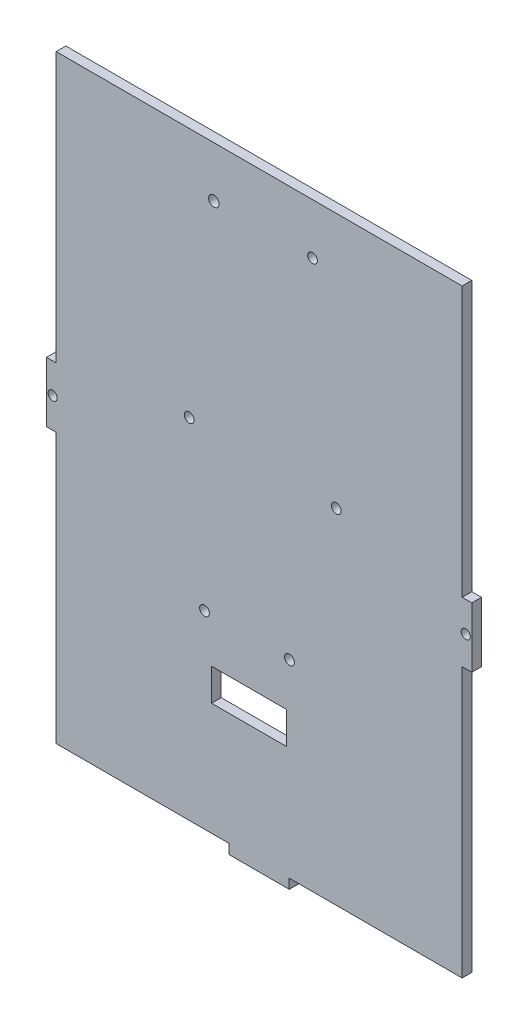
SolidWorks part; units mm, degrees
ref_plane "Front Plane" through (0, 0, 0) normal (0, 0, 1) x (1, 0, 0)
ref_plane "Top Plane" through (0, 0, 0) normal (0, 1, 0) x (1, 0, 0)
ref_plane "Right Plane" through (0, 0, 0) normal (1, 0, 0) x (0, 0, -1)
sketch "Sketch1" plane through (0, 0, 0) normal (0, 0, 1) x (1, 0, 0)
  line L1 (-69.85, 101.6) -> (69.85, 101.6)
  line L2 (-69.85, 101.6) -> (-69.85, -101.6)
  line L3 (-69.85, -101.6) -> (69.85, -101.6)
  line L4 (69.85, 101.6) -> (69.85, -101.6)
  line L5 (-69.85, 101.6) -> (69.85, -101.6) construction
  line L6 (-69.85, -101.6) -> (69.85, 101.6) construction
  point P0 (0, 0)
  dimension "D1" = 203.2
  dimension "D2" = 139.7
extrude "Boss-Extrude1" add sketch "Sketch1" along normal blind 3.18
sketch "Sketch2" plane through (0, 0, 3.18) normal (0, 0, 1) x (1, 0, 0)
  line L0 (0, 0) -> (69.85, 0) construction
  line L1 (-10, 101.6) -> (10, 101.6)
  line L2 (-10, 101.6) -> (-10, 98.42)
  line L3 (-10, 98.42) -> (-1.5, 98.42)
  line L4 (10, 101.6) -> (10, 98.42)
  line L5 (69.85, -101.6) -> (69.85, 101.6) construction
  line L6 (0, 0) -> (0, 101.6) construction
  line L7 (-1.5, 88.42) -> (1.5, 88.42)
  line L8 (-1.5, 88.42) -> (-1.5, 91.42)
  line L10 (1.5, 88.42) -> (1.5, 91.42)
  line L12 (69.85, 101.6) -> (-69.85, 101.6) construction
  line L13 (3.5, 94.42) -> (1.5, 94.42)
  line L14 (3.5, 94.42) -> (3.5, 91.42)
  line L15 (3.5, 91.42) -> (1.5, 91.42)
  line L16 (-3.5, 94.42) -> (-3.5, 91.42)
  line L17 (-10, -101.6) -> (-10, -98.42)
  line L18 (-10, -98.42) -> (-1.5, -98.42)
  line L19 (-1.5, -94.42) -> (-1.5, -98.42)
  line L20 (-1.5, -94.42) -> (-3.5, -94.42)
  line L21 (-3.5, -94.42) -> (-3.5, -91.42)
  line L22 (1.5, 98.42) -> (10, 98.42)
  line L23 (-1.5, 94.42) -> (-3.5, 94.42)
  line L24 (-1.5, -91.42) -> (-3.5, -91.42)
  line L25 (-1.5, -88.42) -> (-1.5, -91.42)
  line L26 (-1.5, -88.42) -> (1.5, -88.42)
  line L27 (-1.5, 91.42) -> (-3.5, 91.42)
  line L28 (1.5, -88.42) -> (1.5, -91.42)
  line L29 (-1.5, 94.42) -> (-1.5, 98.42)
  line L30 (1.5, 94.42) -> (1.5, 98.42)
  line L31 (3.5, -91.42) -> (1.5, -91.42)
  line L32 (3.5, -94.42) -> (3.5, -91.42)
  line L33 (3.5, -94.42) -> (1.5, -94.42)
  line L34 (1.5, -94.42) -> (1.5, -98.42)
  line L35 (1.5, -98.42) -> (10, -98.42)
  line L36 (10, -101.6) -> (10, -98.42)
  line L37 (-10, -101.6) -> (10, -101.6)
  line L38 (-69.85, 101.6) -> (-69.85, -101.6) construction
  line L39 (-69.85, 101.6) -> (-66.67, 101.6)
  line L40 (-69.85, 101.6) -> (-69.85, 9.875)
  line L41 (-69.85, 9.875) -> (-66.67, 9.875)
  line L42 (-66.67, 101.6) -> (-66.67, 9.875)
  line L43 (-69.85, -101.6) -> (-66.67, -101.6)
  line L44 (-69.85, -101.6) -> (-69.85, -9.875)
  line L45 (-69.85, -9.875) -> (-66.67, -9.875)
  line L46 (-66.67, -101.6) -> (-66.67, -9.875)
  line L47 (69.85, -9.875) -> (66.67, -9.875)
  line L48 (66.67, -101.6) -> (66.67, -9.875)
  line L49 (69.85, -101.6) -> (66.67, -101.6)
  line L50 (69.85, -101.6) -> (69.85, -9.875)
  line L51 (69.85, 9.875) -> (66.67, 9.875)
  line L52 (66.67, 101.6) -> (66.67, 9.875)
  line L53 (69.85, 101.6) -> (66.67, 101.6)
  line L54 (69.85, 101.6) -> (69.85, 9.875)
  circle A0 centre (-67.85, 0) radius 1.5
  circle A1 centre (67.85, 0) radius 1.5
  point P0 (0, 50.5662)
  point P5 (0, 32.0079)
  point P10 (15.4931, 34.4893)
  dimension "D11" = 3
  dimension "D12" = 2
  dimension "D1" = 20
  dimension "D2" = 19.75
  dimension "D3" = 4
  dimension "D4" = 3
  dimension "D5" = 3.18
  dimension "D6" = 7
  dimension "D7" = 3
  dimension "D8" = 3
  dimension "D9" = 3.18
  dimension "D10" = 3.18
extrude "Cut-Extrude1" cut sketch "Sketch2" against normal through all
sketch "Sketch3" plane through (0, 0, 0) normal (0, 0, -1) x (-1, 0, 0)
  circle A0 centre (-35.6713, -47.9634) radius 1.59
  circle A1 centre (-35.6713, -30.7773) radius 1.59
extrude "Cut-Extrude2" cut sketch "Sketch3" against normal through all
sketch "Sketch4" plane through (0, 0, 0) normal (0, 0, -1) x (-1, 0, 0)
  circle A0 centre (-34.7507, 80.7361) radius 1.59
  circle A1 centre (-34.7507, 63.55) radius 1.59
  circle A2 centre (36.2498, 80.7361) radius 1.59
  circle A3 centre (36.2498, 63.55) radius 1.59
  circle A4 centre (35.9839, -30.7773) radius 1.59
  circle A5 centre (35.9839, -47.9634) radius 1.59
  circle A6 centre (-35.6713, -30.7773) radius 1.59
  circle A7 centre (-35.6713, -47.9634) radius 1.59
extrude "Cut-Extrude3" cut sketch "Sketch4" against normal through all
sketch "Sketch5" plane through (0, 0, 3.18) normal (0, 0, 1) x (1, 0, 0)
  line L1 (-44.4479, 84.2814) -> (44.4479, 84.2814)
  line L2 (-44.4479, 84.2814) -> (-44.4479, -84.2814)
  line L3 (-44.4479, -84.2814) -> (44.4479, -84.2814)
  line L4 (44.4479, 84.2814) -> (44.4479, -84.2814)
  line L5 (-44.4479, 84.2814) -> (44.4479, -84.2814) construction
  line L6 (-44.4479, -84.2814) -> (44.4479, 84.2814) construction
  point P0 (0, 0)
extrude "Boss-Extrude2" add sketch "Sketch5" against normal blind 3.18
sketch "Sketch6" plane through (0, 0, 3.18) normal (0, 0, 1) x (1, 0, 0)
  line L1 (-10, 101.6) -> (10, 101.6)
  line L2 (-10, 101.6) -> (-10, -101.6)
  line L3 (-10, -101.6) -> (10, -101.6)
  line L4 (10, 101.6) -> (10, -101.6)
extrude "Boss-Extrude3" add sketch "Sketch6" against normal blind 3.18
sketch "Sketch7" plane through (0, 0, 3.18) normal (0, 0, 1) x (1, 0, 0)
  line L0 (0, 0) -> (0, -20.0062) construction
  line L1 (-66.67, -101.6) -> (-9.875, -101.6)
  line L2 (-66.67, -101.6) -> (-66.67, -98.42)
  line L3 (-66.67, -98.42) -> (-9.875, -98.42)
  line L4 (-9.875, -101.6) -> (-9.875, -98.42)
  line L5 (66.67, -101.6) -> (9.875, -101.6)
  line L6 (66.67, -101.6) -> (66.67, -98.42)
  line L7 (66.67, -98.42) -> (9.875, -98.42)
  line L8 (9.875, -101.6) -> (9.875, -98.42)
  dimension "D1" = 3.18
  dimension "D2" = 3.18
  dimension "D3" = 19.75
extrude "Cut-Extrude4" cut sketch "Sketch7" against normal through all
sketch "Sketch8" plane through (0, 0, 3.18) normal (0, 0, 1) x (1, 0, 0)
  line L0 (-66.67, 9.875) -> (-66.67, 101.6) construction
  line L1 (66.67, 101.6) -> (-66.67, 101.6)
  line L2 (66.67, 101.6) -> (66.67, 98.42)
  line L3 (66.67, 98.42) -> (-66.67, 98.42)
  line L4 (-66.67, 101.6) -> (-66.67, 98.42)
  line L5 (-9.875, 98.42) -> (-69.85, 98.42) construction
extrude "Cut-Extrude5" cut sketch "Sketch8" against normal through all
sketch "Sketch9" plane through (0, 0, 3.18) normal (0, 0, 1) x (1, 0, 0)
  circle A0 centre (-17.9479, -36.2051) radius 1.6
  circle A1 centre (25.3331, 14.5259) radius 1.6
  circle A2 centre (-22.9643, 16.203) radius 1.6
  circle A3 centre (9.952, -36.2496) radius 1.6
extrude "Cut-Extrude6" cut sketch "Sketch9" against normal through all
sketch "Sketch10" plane through (0, 0, 3.18) normal (0, 0, 1) x (1, 0, 0)
  line L1 (8.9231, -61.4181) -> (-15.6427, -61.4181)
  line L2 (8.9231, -61.4181) -> (8.9231, -50.8809)
  line L3 (8.9231, -50.8809) -> (-15.6427, -50.8809)
  line L4 (-15.6427, -61.4181) -> (-15.6427, -50.8809)
extrude "Cut-Extrude7" cut sketch "Sketch10" against normal blind 3.18
sketch "Sketch11" plane through (0, 0, 3.18) normal (0, 0, 1) x (1, 0, 0)
  circle A0 centre (17.5239, 81.7974) radius 1.59
  circle A1 centre (-14.8831, 81.7974) radius 1.7179
extrude "Cut-Extrude8" cut sketch "Sketch11" against normal blind 35
